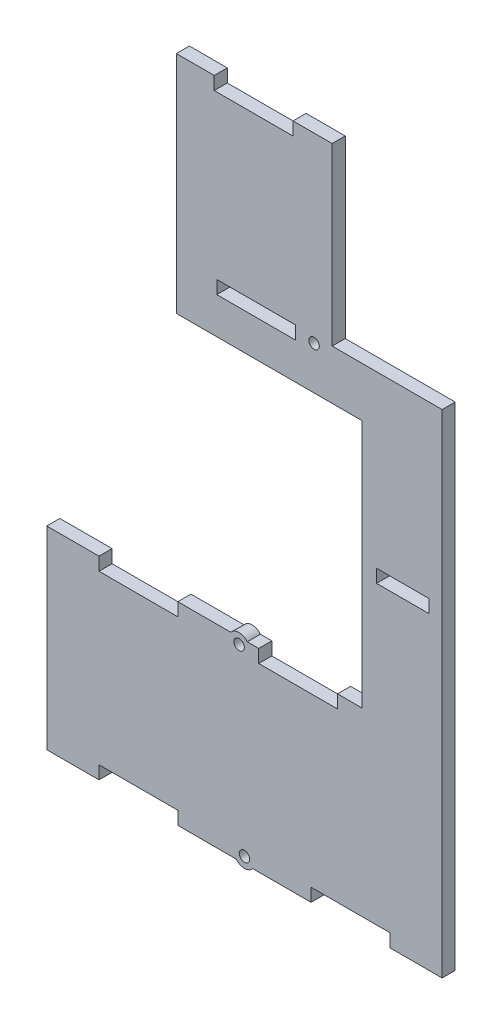
SolidWorks part; units mm, degrees
ref_plane "Front Plane" through (0, 0, 0) normal (0, 0, 1) x (1, 0, 0)
ref_plane "Top Plane" through (0, 0, 0) normal (0, 1, 0) x (1, 0, 0)
ref_plane "Right Plane" through (0, 0, 0) normal (1, 0, 0) x (0, 0, -1)
sketch "Sketch1" plane through (0, 0, 0) normal (0, 0, 1) x (1, 0, 0)
  line L1 (-75.5, 127.5) -> (75.5, 127.5)
  line L2 (-75.5, 127.5) -> (-75.5, -127.5)
  line L3 (-75.5, -127.5) -> (75.5, -127.5)
  line L4 (75.5, 127.5) -> (75.5, -127.5)
  dimension "D1" = 151
  dimension "D2" = 255
  dimension "D3" = 127.5
  dimension "D4" = 75.5
extrude "Boss-Extrude1" add sketch "Sketch1" along normal blind 5
sketch "Sketch2" plane through (0, 0, 5) normal (0, 0, 1) x (1, 0, 0)
  line L1 (-75.5, 127.5) -> (-26.0135, 127.5)
  line L2 (-75.5, 127.5) -> (-75.5, 28.2772)
  line L3 (-75.5, 28.2772) -> (-26.0135, 28.2772)
  line L4 (-26.0135, 127.5) -> (-26.0135, 28.2772)
extrude "Cut-Extrude1" cut sketch "Sketch2" against normal blind 5
sketch "Sketch3" plane through (0, 0, 5) normal (0, 0, 1) x (1, 0, 0)
  line L1 (75.5, 127.5) -> (33.5, 127.5)
  line L2 (75.5, 127.5) -> (75.5, 60.5)
  line L3 (75.5, 60.5) -> (33.5, 60.5)
  line L4 (33.5, 127.5) -> (33.5, 60.5)
  dimension "D1" = 42
  dimension "D2" = 67
extrude "Cut-Extrude2" cut sketch "Sketch3" against normal blind 5
sketch "Sketch4" plane through (0, 0, 5) normal (0, 0, 1) x (1, 0, 0)
  line L0 (-75.5, 28.2772) -> (-75.5, -127.5) construction
  line L1 (-75.5, -53.5) -> (44.85, -53.5)
  line L2 (-75.5, -53.5) -> (-75.5, 41.5472)
  line L3 (-75.5, 41.5472) -> (44.85, 41.5472)
  line L4 (44.85, -53.5) -> (44.85, 41.5472)
  dimension "D1" = 120.35
  dimension "D3" = 95.0472
extrude "Cut-Extrude3" cut sketch "Sketch4" against normal blind 5
sketch "Sketch5" plane through (0, 0, 5) normal (0, 0, 1) x (1, 0, 0)
  line L0 (40.5, -127.5) -> (40.5, -118.9998) construction
  line L1 (-40.5, -127.5) -> (-40.5, -118.9998) construction
  line L2 (20.5, -58.5) -> (20.5, -51.6205) construction
  line L3 (-40.5, -58.5) -> (-40.5, -53.5) construction
  line L5 (60.5, -9.5) -> (60.5, 0) construction
  line L6 (4.475, 55.4958) -> (4.475, 60.5125) construction
  line L7 (3.5, 122.5) -> (3.5, 127.5) construction
  line L8 (25.45, -127.5) -> (55.55, -127.5)
  line L9 (55.55, -127.5) -> (55.55, -122.5)
  line L10 (55.55, -122.5) -> (25.45, -122.5)
  line L11 (25.45, -122.5) -> (25.45, -127.5)
  line L16 (-55.55, -127.5) -> (-25.45, -127.5)
  line L17 (-25.45, -127.5) -> (-25.45, -122.5)
  line L18 (-25.45, -122.5) -> (-55.55, -122.5)
  line L19 (-55.55, -122.5) -> (-55.55, -127.5)
  line L24 (5.45, -58.5) -> (35.55, -58.5)
  line L25 (35.55, -58.5) -> (35.55, -53.5)
  line L26 (35.55, -53.5) -> (5.45, -53.5)
  line L27 (5.45, -53.5) -> (5.45, -58.5)
  line L32 (-55.55, -58.5) -> (-25.45, -58.5)
  line L33 (-25.45, -58.5) -> (-25.45, -53.5)
  line L34 (-25.45, -53.5) -> (-55.55, -53.5)
  line L35 (-55.55, -53.5) -> (-55.55, -58.5)
  line L40 (50.45, -9.5) -> (70.55, -9.5)
  line L41 (70.55, -9.5) -> (70.55, -4.5)
  line L42 (70.55, -4.5) -> (50.45, -4.5)
  line L43 (50.45, -4.5) -> (50.45, -9.5)
  line L48 (-10.575, 55.4958) -> (19.525, 55.4958)
  line L49 (19.525, 55.4958) -> (19.525, 60.5125)
  line L50 (19.525, 60.5125) -> (-10.575, 60.5125)
  line L51 (-10.575, 60.5125) -> (-10.575, 55.4958)
  line L56 (-11.55, 122.5) -> (18.55, 122.5)
  line L57 (18.55, 122.5) -> (18.55, 127.5)
  line L58 (18.55, 127.5) -> (-11.55, 127.5)
  line L59 (-11.55, 127.5) -> (-11.55, 122.5)
  point P40 (19.525, 58.0042)
  dimension "D1" = 15.05
  dimension "D8" = 5
  dimension "D2" = 15.05
  dimension "D3" = 15.05
  dimension "D4" = 15.05
  dimension "D5" = 10.05
  dimension "D6" = 15.05
  dimension "D7" = 15.05
extrude "Cut-Extrude4" cut sketch "Sketch5" against normal blind 5
sketch "Sketch6" plane through (0, 0, 5) normal (0, 0, 1) x (1, 0, 0)
  circle A0 centre (0, -125) radius 2
  circle A1 centre (-2.045, -56) radius 2
  circle A2 centre (26.5785, 58) radius 2
  dimension "D1" = 4
  dimension "D2" = 4
  dimension "D3" = 4
extrude "Cut-Extrude5" cut sketch "Sketch6" against normal blind 10
sketch "Sketch8" plane through (0, 0, 5) normal (0, 0, 1) x (1, 0, 0)
  circle A0 centre (0, -125) radius 2
  circle A1 centre (0, -125) radius 4
  circle A2 centre (-2.045, -56) radius 2
  circle A3 centre (-2.045, -56) radius 4
  dimension "D1" = 8
  dimension "D2" = 8
extrude "Boss-Extrude2" add sketch "Sketch8" against normal blind 5
